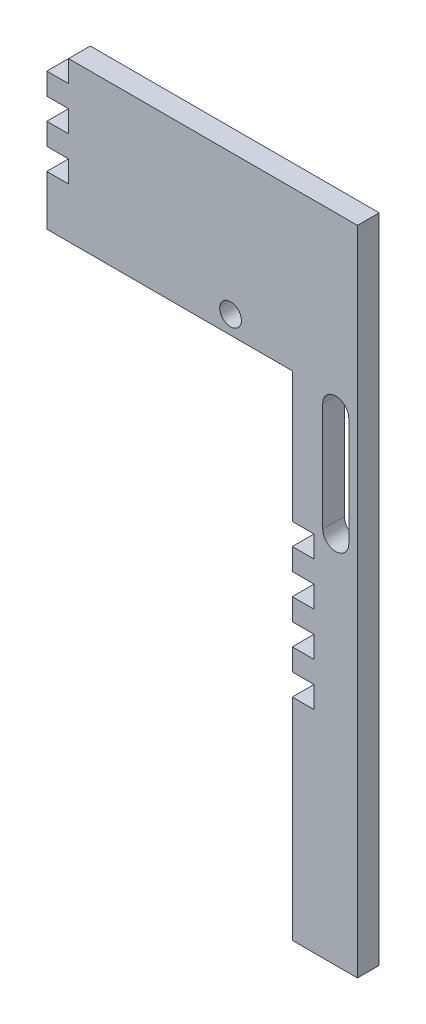
SolidWorks part; units mm, degrees
ref_plane "Plan de face" through (0, 0, 0) normal (0, 0, 1) x (1, 0, 0)
ref_plane "Plan de dessus" through (0, 0, 0) normal (0, 1, 0) x (1, 0, 0)
ref_plane "Plan de droite" through (0, 0, 0) normal (1, 0, 0) x (0, 0, -1)
sketch "Esquisse1" plane through (0, 0, 0) normal (0, 0, 1) x (1, 0, 0)
  line L0 (0, 0) -> (-30, 0)
  line L1 (-30, 0) -> (-30, 227)
  line L2 (0, 0) -> (0, 300)
  line L3 (0, 300) -> (-143, 300)
  line L4 (-143, 227) -> (-143, 300)
  line L5 (-30, 227) -> (-143, 227)
  dimension "D1" = 143
  dimension "D2" = 73
  dimension "D3" = 300
  dimension "D4" = 30
extrude "Boss.-Extru.1" add sketch "Esquisse1" along normal blind 10
sketch "Esquisse2" plane through (0, 0, 10) normal (0, 0, 1) x (1, 0, 0)
  line L1 (-143, 300) -> (-133, 300)
  line L2 (-143, 300) -> (-143, 290)
  line L3 (-143, 290) -> (-133, 290)
  line L4 (-133, 300) -> (-133, 290)
  dimension "D1" = 10
  dimension "D2" = 10
extrude "Enlèv. mat.-Extru.1" cut sketch "Esquisse2" against normal blind 10
pattern_linear "Répétition linéaire1" count 3 spacing 20 along (0, -1, 0) of "Enlèv. mat.-Extru.1"
sketch "Esquisse3" plane through (0, 0, 10) normal (0, 0, 1) x (1, 0, 0)
  line L0 (-30, 227) -> (-30, 0) construction
  line L1 (-30, 167) -> (-20, 167)
  line L2 (-30, 167) -> (-30, 157)
  line L3 (-30, 157) -> (-20, 157)
  line L4 (-20, 167) -> (-20, 157)
  line L5 (-143, 227) -> (-30, 227) construction
  dimension "D1" = 10
  dimension "D2" = 10
  dimension "D3" = 60
extrude "Enlèv. mat.-Extru.2" cut sketch "Esquisse3" against normal blind 10
pattern_linear "Répétition linéaire2" count 4 spacing 20 along (0, -1, 0) of "Enlèv. mat.-Extru.2"
sketch "Esquisse4" plane through (0, 0, 10) normal (0, 0, 1) x (1, 0, 0)
  line L0 (-4, 221) -> (-4, 171)
  line L2 (-16, 171) -> (-16, 221)
  line L4 (-143, 227) -> (-30, 227) construction
  line L5 (0, 0) -> (0, 300) construction
  arc A0 (-16, 221) -> (-4, 221) centre (-10, 221) cw
  arc A1 (-16, 171) -> (-4, 171) centre (-10, 171) ccw
  dimension "D4" = 6
  dimension "D5" = 6
  dimension "D1" = 12
  dimension "D2" = 50
  dimension "D3" = 4
extrude "Enlèv. mat.-Extru.3" cut sketch "Esquisse4" against normal blind 10
sketch "Esquisse5" plane through (0, 0, 10) normal (0, 0, 1) x (1, 0, 0)
  circle A0 centre (-58.4159, 235.3705) radius 5
  dimension "D1" = 10
extrude "Enlèv. mat.-Extru.4" cut sketch "Esquisse5" against normal blind 10
